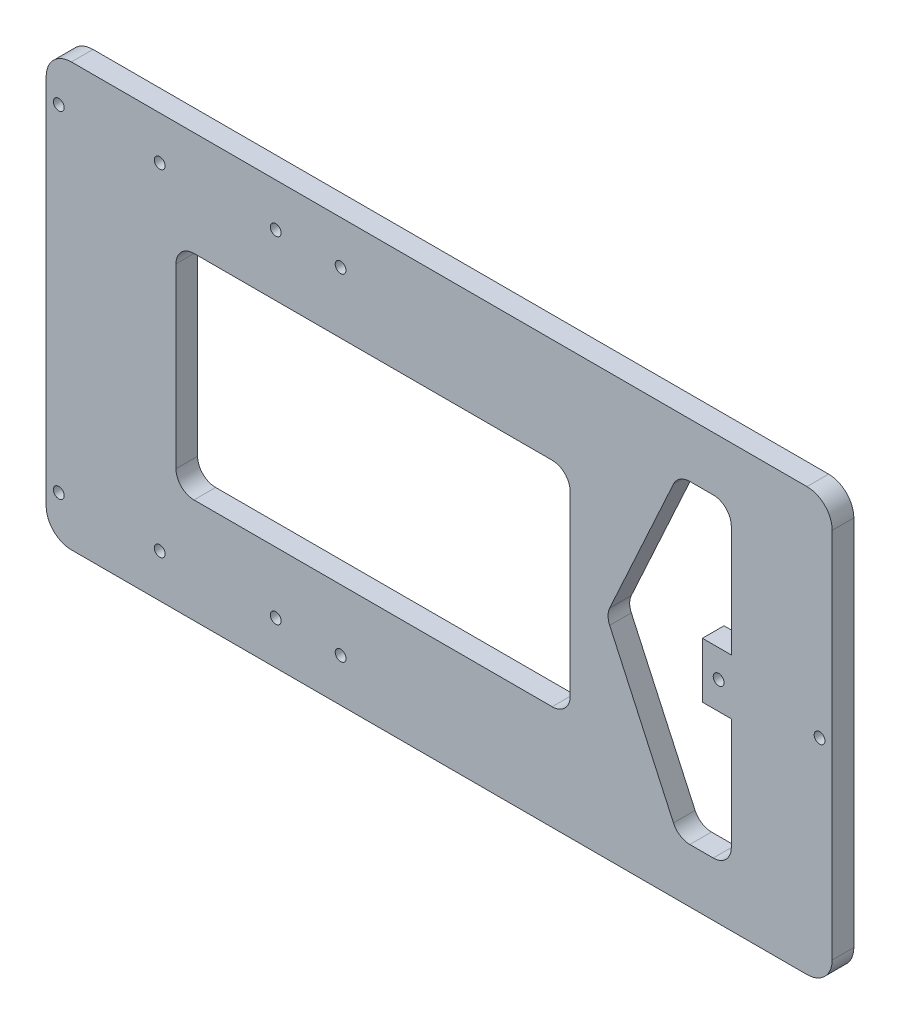
SolidWorks part; units mm, degrees
ref_plane "Front Plane" through (0, 0, 0) normal (0, 0, 1) x (1, 0, 0)
ref_plane "Top Plane" through (0, 0, 0) normal (0, 1, 0) x (1, 0, 0)
ref_plane "Right Plane" through (0, 0, 0) normal (1, 0, 0) x (0, 0, -1)
sketch "Sketch1" plane through (0, 0, 0) normal (0, 0, 1) x (1, 0, 0)
  line L0 (-242.1092, 256.3436) -> (-242.1092, 139.1436) construction
  line L1 (-59.1092, 256.3436) -> (-59.1092, 139.1436) construction
  line L2 (-242.1092, 139.1436) -> (-59.1092, 139.1436) construction
  line L3 (-150.6092, 256.3436) -> (-150.6092, 306.7436) construction
  line L4 (-238.1092, 139.1436) -> (-246.1092, 139.1436) construction
  line L5 (-242.1092, 256.3436) -> (-59.1092, 256.3436) construction
  line L6 (-238.1092, 139.1436) -> (-238.1092, 256.3436) construction
  line L7 (-238.1092, 256.3436) -> (-246.1092, 256.3436) construction
  line L8 (-246.1092, 139.1436) -> (-246.1092, 256.3436) construction
  line L9 (-238.1092, 139.1436) -> (-246.1092, 256.3436) construction
  line L10 (-238.1092, 256.3436) -> (-246.1092, 139.1436) construction
  line L11 (-55.1092, 139.1436) -> (-63.1092, 139.1436) construction
  line L12 (-55.1092, 139.1436) -> (-55.1092, 256.3436) construction
  line L13 (-55.1092, 256.3436) -> (-63.1092, 256.3436) construction
  line L14 (-63.1092, 139.1436) -> (-63.1092, 256.3436) construction
  line L15 (-55.1092, 139.1436) -> (-63.1092, 256.3436) construction
  line L16 (-55.1092, 256.3436) -> (-63.1092, 139.1436) construction
  line L17 (-231.6092, 232.3436) -> (-252.6092, 232.3436)
  line L18 (-231.6092, 232.3436) -> (-231.6092, 256.3436)
  line L19 (-231.6092, 256.3436) -> (-252.6092, 256.3436)
  line L20 (-252.6092, 232.3436) -> (-252.6092, 256.3436)
  line L21 (-231.6092, 232.3436) -> (-252.6092, 256.3436) construction
  line L22 (-231.6092, 256.3436) -> (-252.6092, 232.3436) construction
  line L23 (-252.6092, 163.1436) -> (-231.6092, 163.1436)
  line L24 (-252.6092, 163.1436) -> (-252.6092, 139.1436)
  line L25 (-252.6092, 139.1436) -> (-231.6092, 139.1436)
  line L26 (-231.6092, 163.1436) -> (-231.6092, 139.1436)
  line L27 (-252.6092, 163.1436) -> (-231.6092, 139.1436) construction
  line L28 (-252.6092, 139.1436) -> (-231.6092, 163.1436) construction
  line L29 (-48.6092, 185.7436) -> (-69.6092, 185.7436) construction
  line L30 (-48.6092, 185.7436) -> (-48.6092, 209.7436) construction
  line L31 (-48.6092, 209.7436) -> (-69.6092, 209.7436) construction
  line L32 (-69.6092, 185.7436) -> (-69.6092, 209.7436) construction
  line L33 (-48.6092, 185.7436) -> (-69.6092, 209.7436) construction
  line L34 (-48.6092, 209.7436) -> (-69.6092, 185.7436) construction
  line L35 (-150.6092, 306.7436) -> (-259.6092, 306.7436) construction
  line L37 (-259.6092, 256.3436) -> (-41.6092, 256.3436)
  line L38 (-259.6092, 306.7436) -> (-41.6092, 306.7436)
  line L39 (-259.6092, 306.7436) -> (-259.6092, 88.7436)
  line L40 (-259.6092, 88.7436) -> (-41.6092, 88.7436)
  line L41 (-41.6092, 306.7436) -> (-41.6092, 88.7436)
  line L42 (-259.6092, 256.3436) -> (-259.6092, 139.1436)
  line L43 (-259.6092, 139.1436) -> (-41.6092, 139.1436)
  line L44 (-41.6092, 256.3436) -> (-41.6092, 139.1436)
  circle A0 centre (-269.6092, 244.3436) radius 2.5
  circle A1 centre (-31.6092, 197.7436) radius 2.5
  circle A3 centre (-269.6092, 151.1436) radius 2.5
  circle A6 centre (-256.1092, 244.3436) radius 1.5
  circle A7 centre (-256.1092, 151.1436) radius 1.5
  circle A8 centre (-45.1092, 197.7436) radius 1.5
  circle A9 centre (-73.1092, 197.7436) radius 1.5
  circle A10 centre (-228.1092, 244.3436) radius 1.5
  circle A11 centre (-228.1092, 151.1436) radius 1.5
  point P0 (-242.1092, 197.7436)
  point P9 (-59.1092, 197.7436)
  point P14 (-242.1092, 244.3436)
  point P19 (-242.1092, 151.1436)
  point P24 (-59.1092, 197.7436)
  point P34 (-150.6092, 197.7436)
  dimension "D11" = 5
  dimension "D12" = 10
  dimension "D15" = 3
  dimension "D20" = 5
  dimension "D21" = 10
  dimension "D22" = 5
  dimension "D23" = 3.5
  dimension "D24" = 3.5
  dimension "D1" = 183
  dimension "D2" = 8
  dimension "D3" = 8
  dimension "D4" = 21
  dimension "D5" = 24
  dimension "D6" = 117.2
  dimension "D7" = 21
  dimension "D8" = 24
  dimension "D9" = 21
  dimension "D10" = 24
  dimension "D16" = 109
  dimension "D17" = 109
  dimension "D18" = 218
  dimension "D19" = 218
extrude "Boss-Extrude1" add sketch "Sketch1" along normal blind 6 contours A6 | A10 | A11 | A8 | A9 | L37 L44 L43 L42 | A7
sketch "Sketch2" plane through (0, 0, 6) normal (0, 0, 1) x (1, 0, 0)
  line L0 (-259.6092, 256.3436) -> (-41.6092, 256.3436) construction
  line L1 (-259.6092, 256.3436) -> (-41.6092, 256.3436)
  line L2 (-186.9425, 273.3122) -> (-186.9425, 128.0805) construction
  line L3 (-259.6092, 256.3436) -> (-259.6092, 139.1436) construction
  line L4 (-256.1092, 244.3436) -> (-152.9234, 244.3436) construction
  line L5 (-256.1092, 151.1436) -> (-151.5972, 151.1436) construction
  circle A1 centre (-195.9425, 151.1436) radius 1.5
  circle A2 centre (-177.9425, 151.1436) radius 1.5
  circle A3 centre (-195.9425, 244.3436) radius 1.5
  circle A4 centre (-177.9425, 244.3436) radius 1.5
  dimension "D2" = 9
  dimension "D3" = 3
  dimension "D4" = 9
  dimension "D5" = 9
  dimension "D6" = 9
  dimension "D1" = 72.6667
extrude "Cut-Extrude1" cut sketch "Sketch2" against normal blind 6 contours A1 | A2 | A3 | A4
fillet "Fillet1" radius 7 4 edges at (-41.6092, 139.1436, 3) (-41.6092, 256.3436, 3) (-259.6092, 139.1436, 3) (-259.6092, 256.3436, 3)
sketch "Sketch3" plane through (0, 0, 0) normal (0, 0, -1) x (-1, 0, 0)
  line L0 (223.6092, 227.3436) -> (223.6092, 168.1436)
  line L1 (223.6092, 227.3436) -> (114.2758, 227.3436)
  line L2 (114.2758, 227.3436) -> (114.2758, 168.1436)
  line L3 (114.2758, 168.1436) -> (223.6092, 168.1436)
  line L5 (231.6092, 232.3436) -> (235.6283, 232.3436) construction
  line L6 (249.6092, 163.1436) -> (234.6092, 163.1436) construction
  line L7 (41.6092, 249.3436) -> (41.6092, 146.1436) construction
  dimension "D1" = 5
  dimension "D2" = 5
  dimension "D3" = 72.6667
extrude "Cut-Extrude2" cut sketch "Sketch3" against normal blind 10
fillet "Fillet3" radius 5 4 edges at (-114.2758, 168.1436, 3) (-223.6092, 168.1436, 3) (-223.6092, 227.3436, 3) (-114.2758, 227.3436, 3)
sketch "Sketch4" plane through (0, 0, 0) normal (0, 0, -1) x (-1, 0, 0)
  line L0 (84.299, 241.3436) -> (69.5973, 241.3436)
  line L1 (69.5973, 205.4186) -> (69.5973, 241.3436)
  line L2 (69.5973, 205.4186) -> (77.6092, 205.4186)
  line L3 (77.6092, 205.4186) -> (77.6092, 190.0686)
  line L4 (77.6092, 190.0686) -> (69.5973, 190.0686)
  line L5 (69.5973, 190.0686) -> (69.5973, 154.1436)
  line L6 (69.5973, 154.1436) -> (84.299, 154.1436)
  line L7 (84.299, 154.1436) -> (104.2758, 197.7436)
  line L8 (104.2758, 197.7436) -> (84.299, 241.3436)
  line L9 (252.6092, 256.3436) -> (48.6092, 256.3436) construction
  line L10 (252.6092, 139.1436) -> (48.6092, 139.1436) construction
  line L11 (114.2758, 222.3436) -> (114.2758, 173.1436) construction
  dimension "D1" = 15
  dimension "D2" = 15
  dimension "D3" = 10
extrude "Cut-Extrude3" cut sketch "Sketch4" against normal blind 10
fillet "Fillet4" radius 5 5 edges at (-69.5973, 154.1436, 3) (-84.299, 154.1436, 3) (-104.2758, 197.7436, 3) (-84.299, 241.3436, 3) (-69.5973, 241.3436, 3)
